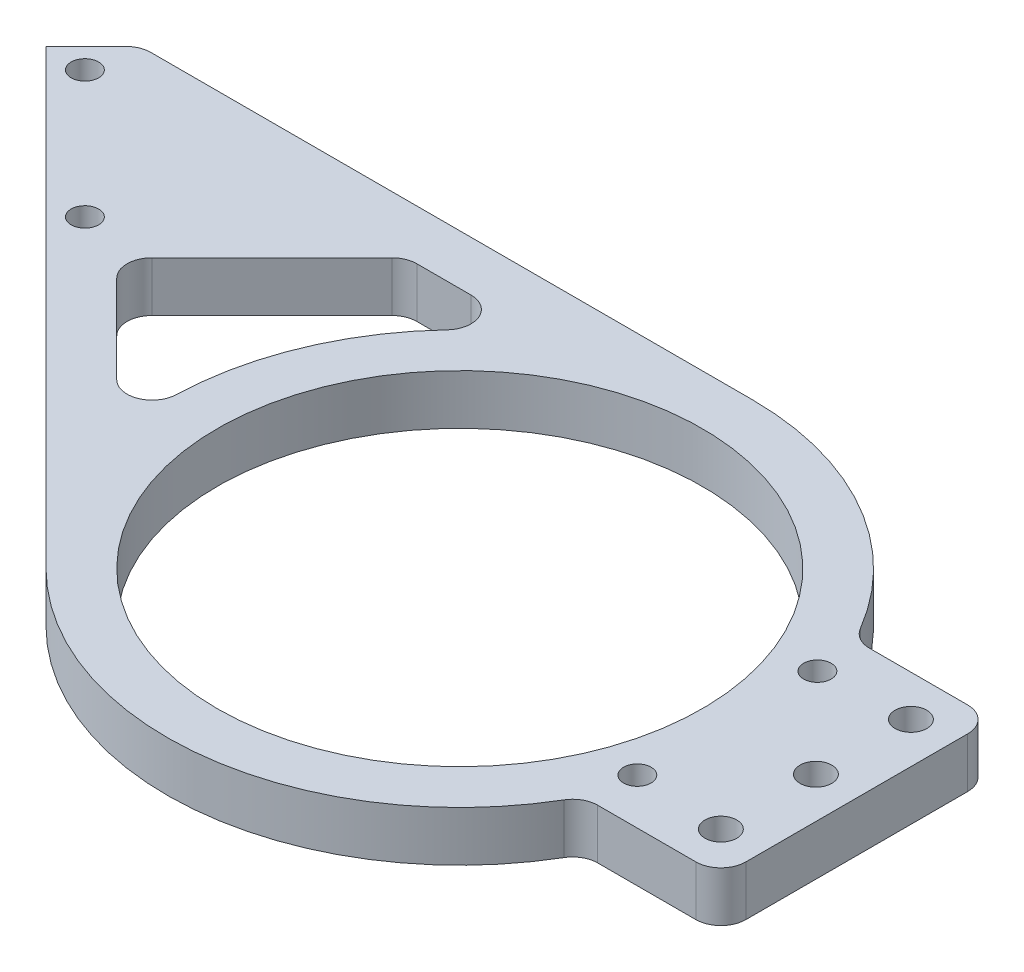
SolidWorks part; units mm, degrees
material "1060 Alloy"
ref_plane "Front Plane" through (0, 0, 0) normal (0, 0, 1) x (1, 0, 0)
ref_plane "Top Plane" through (0, 0, 0) normal (0, 1, 0) x (1, 0, 0)
ref_plane "Right Plane" through (0, 0, 0) normal (1, 0, 0) x (0, 0, -1)
sketch "Sketch1" plane through (0, 0, 0) normal (0, 1, 0) x (1, 0, 0)
  line L0 (0, 0) -> (58.5, 0) construction
  line L4 (48.5, 18) -> (48.5, -18) construction
  line L5 (-131.787, 49.0555) -> (-102.2653, 19.5338) construction
  line L6 (-102.2653, 19.5338) -> (-170.8547, -49.0555) construction
  line L7 (-170.8547, -49.0555) -> (-200.3764, -19.5338) construction
  line L8 (-200.3764, -19.5338) -> (-131.787, 49.0555) construction
  line L9 (-81.6517, -1.0798) -> (-14.4422, -68.2893) construction
  line L10 (-163.9272, -55.983) -> (-126.5132, -93.397) construction
  line L11 (-136.56, -14.7609) -> (-166.0817, 14.7609) construction
  line L12 (-151.3209, 0) -> (0, 0) construction
  line L14 (-63.2991, 58.5) -> (-102.2653, 19.5338) construction
  line L15 (-102.2653, 19.5338) -> (-41.3657, -41.3657)
  line L17 (-122.3426, 58.5) -> (0, 58.5)
  line L18 (-88.1232, 19.5338) -> (-57.4247, -11.1646)
  line L19 (-88.1232, 19.5338) -> (-59.157, 48.5)
  line L20 (-59.157, 48.5) -> (-32.7109, 48.5)
  line L21 (71.2, 9.5) -> (71.2, -9.5) construction
  line L22 (71.2, 9.5) -> (71.2, 28.5) construction
  line L23 (71.2, -9.5) -> (71.2, -28.5) construction
  line L24 (51.8051, 27.175) -> (79.375, 27.175)
  line L25 (79.375, 27.175) -> (79.375, -27.175)
  line L26 (51.8051, -27.175) -> (79.375, -27.175)
  line L30 (-131.787, 49.0555) -> (-102.2653, 19.5338)
  line L31 (-131.787, 49.0555) -> (-122.3426, 58.5)
  line L32 (-98.3762, 23.4229) -> (-127.8979, 52.9446) construction
  line L33 (48.5, 18) -> (58.5, 18) construction
  line L34 (58.5, 18) -> (58.5, -18) construction
  line L35 (48.5, -18) -> (58.5, -18) construction
  circle A0 centre (0, 0) radius 48.5
  arc A1 (51.8051, 27.175) -> (0, 58.5) centre (0, 0) ccw
  circle A2 centre (0, 0) radius 48.5 construction
  circle A3 centre (71.2, 9.5) radius 3.175 construction
  circle A4 centre (71.2, -9.5) radius 3.175 construction
  circle A7 centre (71.2, 19) radius 3.175 construction
  circle A8 centre (71.2, 0) radius 3.175 construction
  circle A9 centre (71.2, -19) radius 3.175 construction
  arc A10 (-32.7109, 48.5) -> (-57.4247, -11.1646) centre (0, 0) ccw
  arc A11 (-41.3657, -41.3657) -> (51.8051, -27.175) centre (0, 0) ccw
  circle A12 centre (-123.8321, 48.8788) radius 2.75
  circle A13 centre (-98.3762, 23.4229) radius 2.75
  circle A14 centre (53.5, 9.5) radius 2.75 construction
  circle A15 centre (53.5, 18) radius 2.75
  circle A16 centre (53.5, -18) radius 2.75
  point P3 (71.2, 28.5)
  point P4 (14.5, 0)
  point P8 (14.5, 0)
  point P33 (71.2, 0)
  point P48 (71.2, 19)
  point P49 (71.2, 0)
  point P52 (79.375, 0)
  point P53 (71.2, -19)
  point P54 (71.2, -28.5)
  point P57 (48.5, 0)
  dimension "D1" = 97
  dimension "D2" = 10
  dimension "D13" = 6.35
  dimension "D15" = 9.5
  dimension "D16" = 5
  dimension "D17" = 5
  dimension "D8" = 5.5
  dimension "D9" = 5.5
  dimension "D19" = 36
  dimension "D4" = 5.5
  dimension "D3" = 5.75
  dimension "D22" = 5.5
  dimension "D5" = 41.75
  dimension "D6" = 97
  dimension "D7" = 45
  dimension "D10" = 10
  dimension "D11" = 10
  dimension "D12" = 10
  dimension "D14" = 19
  dimension "D18" = 5.5
  dimension "D20" = 10
  dimension "D21" = 5
  dimension "D23" = 12.7
extrude "Boss-Extrude1" add sketch "Sketch1" against normal mid plane 10
hole_wizard "1/4 (0.25) Diameter Hole1" positions "Sketch9" profile "Sketch10" hole size "1/4" standard "ANSI Inch" end condition through all
sketch "Sketch9" plane through (0, 5, 0) normal (0, 1, 0) x (1, 0, 0)
  point P3 (71.2, 19)
  point P6 (71.2, 0)
  point P9 (71.2, -19)
sketch "Sketch10" plane through (71.2, 5, -19) normal (1, 0, 0) x (0, 0, 1)
  line L0 (0, 0) -> (0, 10)
  line L1 (0, 10) -> (3.175, 10)
  line L2 (3.175, 10) -> (3.175, 0)
  line L5 (3.175, 0) -> (0, 0)
  line L11 (0, -6.35) -> (0, 107.95) construction
  dimension "Thru Hole Dia." = 6.35
  dimension "Thru Hole Depth" = 10
fillet "Fillet1" radius 5 9 edges at (79.375, 0, -27.175) (79.375, 0, 27.175) (51.8051, 0, 27.175) (51.8051, 0, -27.175) (-88.1232, 0, -19.5338) (-59.157, 0, -48.5) (-57.4247, 0, 11.1646) (-32.7109, 0, -48.5) (-122.3426, 0, -58.5)
